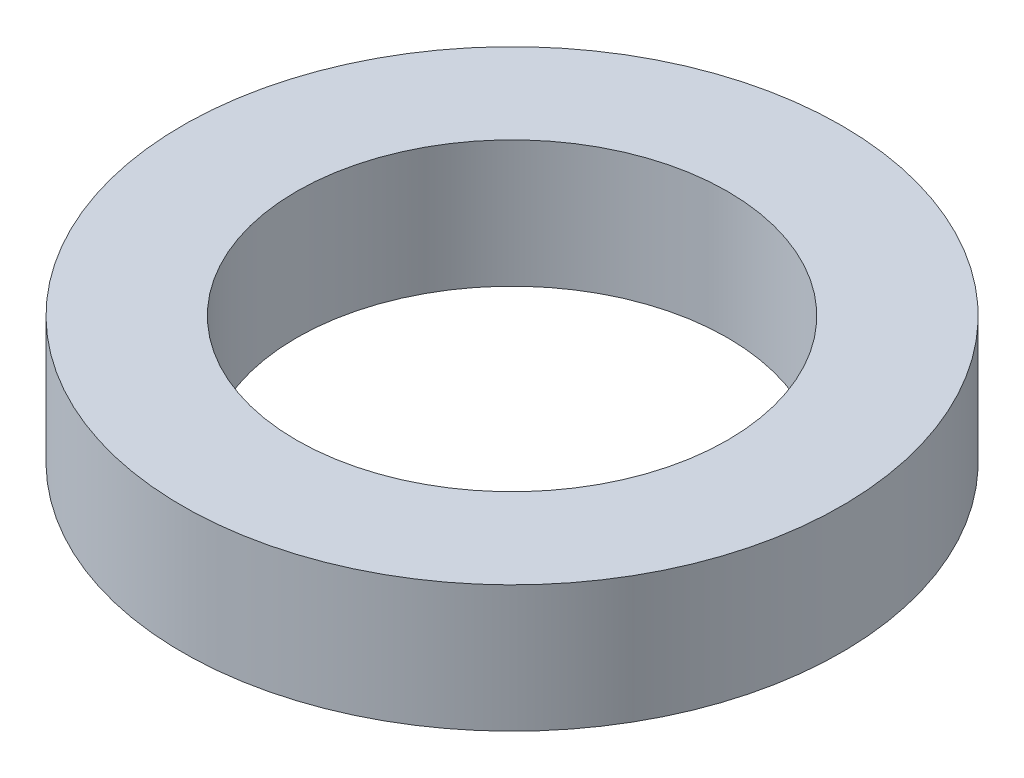
SolidWorks part; units mm, degrees
ref_plane "Front Plane" through (0, 0, 0) normal (0, 0, 1) x (1, 0, 0)
ref_plane "Top Plane" through (0, 0, 0) normal (0, 1, 0) x (1, 0, 0)
ref_plane "Right Plane" through (0, 0, 0) normal (1, 0, 0) x (0, 0, -1)
sketch "Sketch1" plane through (0, 0, 0) normal (0, 0, 1) x (1, 0, 0)
  line L0 (0, 0) -> (0, 23368.9604) construction
  line L2 (8.5, 0) -> (13, 0)
  line L3 (8.5, 0) -> (8.5, 5)
  line L4 (8.5, 5) -> (13, 5)
  line L5 (13, 0) -> (13, 5)
  dimension "D1" = 17
  dimension "D2" = 26
  dimension "D3" = 5
revolve "Revolve1" add sketch "Sketch1" angle 360 about L0
